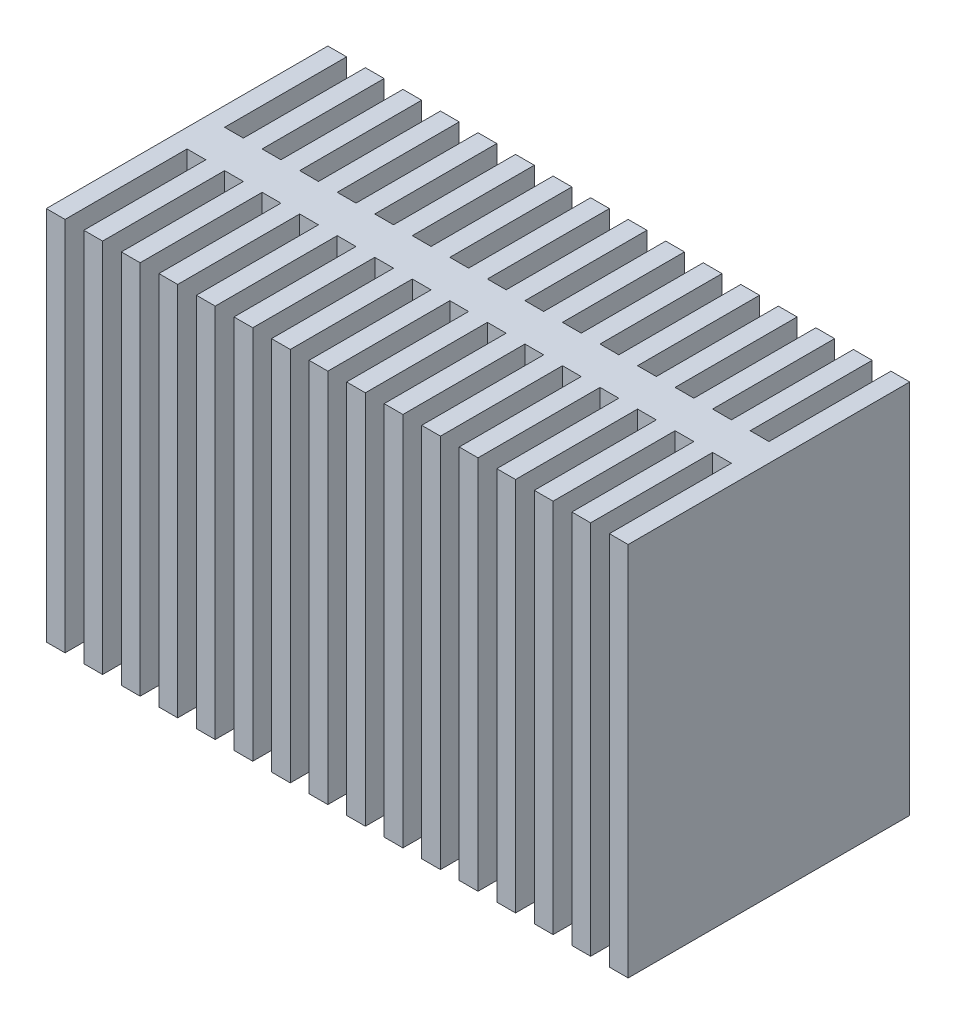
SolidWorks part; units mm, degrees
material "6061 Alloy"
ref_plane "Front Plane" through (0, 0, 0) normal (0, 0, 1) x (1, 0, 0)
ref_plane "Top Plane" through (0, 0, 0) normal (0, 1, 0) x (1, 0, 0)
ref_plane "Right Plane" through (0, 0, 0) normal (1, 0, 0) x (0, 0, -1)
sketch "Sketch2" plane through (0, 0, 0) normal (0, 1, 0) x (1, 0, 0)
  line L0 (0, 0) -> (0, -15)
  line L1 (0, -15) -> (1, -15)
  line L2 (1, -15) -> (1, -8.5)
  line L3 (1, -8.5) -> (2, -8.5)
  line L4 (2, -8.5) -> (2, -6.5)
  line L5 (2, -6.5) -> (1, -6.5)
  line L6 (1, -6.5) -> (1, 0)
  line L7 (1, 0) -> (0, 0)
  line L8 (3, 0) -> (2, 0)
  line L9 (2, 0) -> (2, -15)
  line L10 (2, -15) -> (3, -15)
  line L11 (3, -15) -> (3, -8.5)
  line L12 (3, -8.5) -> (4, -8.5)
  line L13 (4, -8.5) -> (4, -6.5)
  line L14 (4, -6.5) -> (3, -6.5)
  line L15 (3, -6.5) -> (3, 0)
  line L16 (5, 0) -> (4, 0)
  line L17 (4, 0) -> (4, -15)
  line L18 (4, -15) -> (5, -15)
  line L19 (5, -15) -> (5, -8.5)
  line L20 (5, -8.5) -> (6, -8.5)
  line L21 (6, -8.5) -> (6, -6.5)
  line L22 (6, -6.5) -> (5, -6.5)
  line L23 (5, -6.5) -> (5, 0)
  line L24 (7, 0) -> (6, 0)
  line L25 (6, 0) -> (6, -15)
  line L26 (6, -15) -> (7, -15)
  line L27 (7, -15) -> (7, -8.5)
  line L28 (7, -8.5) -> (8, -8.5)
  line L29 (8, -8.5) -> (8, -6.5)
  line L30 (8, -6.5) -> (7, -6.5)
  line L31 (7, -6.5) -> (7, 0)
  line L32 (9, 0) -> (8, 0)
  line L33 (8, 0) -> (8, -15)
  line L34 (8, -15) -> (9, -15)
  line L35 (9, -15) -> (9, -8.5)
  line L36 (9, -8.5) -> (10, -8.5)
  line L37 (10, -8.5) -> (10, -6.5)
  line L38 (10, -6.5) -> (9, -6.5)
  line L39 (9, -6.5) -> (9, 0)
  line L40 (11, 0) -> (10, 0)
  line L41 (10, 0) -> (10, -15)
  line L42 (10, -15) -> (11, -15)
  line L43 (11, -15) -> (11, -8.5)
  line L44 (11, -8.5) -> (12, -8.5)
  line L45 (12, -8.5) -> (12, -6.5)
  line L46 (12, -6.5) -> (11, -6.5)
  line L47 (11, -6.5) -> (11, 0)
  line L48 (12, -15) -> (12, 0)
  line L49 (12, 0) -> (13, 0)
  line L50 (13, 0) -> (13, -15)
  line L51 (13, -15) -> (12, -15)
  line L52 (13, 0) -> (12, 0)
  line L53 (12, 0) -> (12, -15)
  line L54 (12, -15) -> (13, -15)
  line L55 (13, -15) -> (13, -8.5)
  line L56 (13, -8.5) -> (14, -8.5)
  line L57 (14, -8.5) -> (14, -6.5)
  line L58 (14, -6.5) -> (13, -6.5)
  line L59 (13, -6.5) -> (13, 0)
  line L60 (15, 0) -> (14, 0)
  line L61 (14, 0) -> (14, -15)
  line L62 (14, -15) -> (15, -15)
  line L63 (15, -15) -> (15, -8.5)
  line L64 (15, -8.5) -> (16, -8.5)
  line L65 (16, -8.5) -> (16, -6.5)
  line L66 (16, -6.5) -> (15, -6.5)
  line L67 (15, -6.5) -> (15, 0)
  line L68 (17, 0) -> (16, 0)
  line L69 (16, 0) -> (16, -15)
  line L70 (16, -15) -> (17, -15)
  line L71 (17, -15) -> (17, -8.5)
  line L72 (17, -8.5) -> (18, -8.5)
  line L73 (18, -8.5) -> (18, -6.5)
  line L74 (18, -6.5) -> (17, -6.5)
  line L75 (17, -6.5) -> (17, 0)
  line L76 (19, 0) -> (18, 0)
  line L77 (18, 0) -> (18, -15)
  line L78 (18, -15) -> (19, -15)
  line L79 (19, -15) -> (19, -8.5)
  line L80 (19, -8.5) -> (20, -8.5)
  line L81 (20, -8.5) -> (20, -6.5)
  line L82 (20, -6.5) -> (19, -6.5)
  line L83 (19, -6.5) -> (19, 0)
  line L84 (21, 0) -> (20, 0)
  line L85 (20, 0) -> (20, -15)
  line L86 (20, -15) -> (21, -15)
  line L87 (21, -15) -> (21, -8.5)
  line L88 (21, -8.5) -> (22, -8.5)
  line L89 (22, -8.5) -> (22, -6.5)
  line L90 (22, -6.5) -> (21, -6.5)
  line L91 (21, -6.5) -> (21, 0)
  line L92 (23, 0) -> (22, 0)
  line L93 (22, 0) -> (22, -15)
  line L94 (22, -15) -> (23, -15)
  line L95 (23, -15) -> (23, -8.5)
  line L96 (23, -8.5) -> (24, -8.5)
  line L97 (24, -8.5) -> (24, -6.5)
  line L98 (24, -6.5) -> (23, -6.5)
  line L99 (23, -6.5) -> (23, 0)
  line L100 (25, 0) -> (24, 0)
  line L101 (24, 0) -> (24, -15)
  line L102 (24, -15) -> (25, -15)
  line L103 (25, -15) -> (25, -8.5)
  line L104 (25, -8.5) -> (26, -8.5)
  line L105 (26, -8.5) -> (26, -6.5)
  line L106 (26, -6.5) -> (25, -6.5)
  line L107 (25, -6.5) -> (25, 0)
  line L108 (27, 0) -> (26, 0)
  line L109 (26, 0) -> (26, -15)
  line L110 (26, -15) -> (27, -15)
  line L111 (27, -15) -> (27, -8.5)
  line L112 (27, -8.5) -> (28, -8.5)
  line L113 (28, -8.5) -> (28, -6.5)
  line L114 (28, -6.5) -> (27, -6.5)
  line L115 (27, -6.5) -> (27, 0)
  line L116 (29, 0) -> (28, 0)
  line L117 (28, 0) -> (28, -15)
  line L118 (28, -15) -> (29, -15)
  line L119 (29, -15) -> (29, -8.5)
  line L120 (29, -8.5) -> (30, -8.5)
  line L121 (30, -8.5) -> (30, -6.5)
  line L122 (30, -6.5) -> (29, -6.5)
  line L123 (29, -6.5) -> (29, 0)
  line L124 (30, -8.5) -> (30, -15)
  line L125 (30, -15) -> (31, -15)
  line L126 (31, -15) -> (31, 0)
  line L127 (31, 0) -> (30, 0)
  line L128 (30, 0) -> (30, -6.5)
  line L129 (30, -6.5) -> (30, -8.5)
  line L130 (30, 0) -> (30, -15)
  dimension "D1" = 15
  dimension "D2" = 2
  dimension "D3" = 6.5
  dimension "D4" = 1
  dimension "D5" = 1
  dimension "D6" = 2
  dimension "D7" = 15
extrude "Boss-Extrude1" add sketch "Sketch2" along normal blind 20 contours L6 L7 L0 L1 L2 L3 L4 L5 | L14 L15 L8 L9 L4 L10 L11 L12 L13 | L22 L23 L16 L17 L13 L18 L19 L20 L21 | L30 L31 L24 L25 L21 L26 L27 L28 L29 | L38 L39 L32 L33 L29 L34 L35 L36 L37 | L46 L47 L40 L41 L37 L42 L43 L44 L45 | L51 L50 L49 L48 L45 | L127 L128 L121 L124 L125 L126 | L52 L53 L54 L55 L56 L57 L58 L59 | L60 L61 L62 L63 L64 L65 L66 L67 | L68 L69 L70 L71 L72 L73 L74 L75 | L76 L77 L78 L79 L80 L81 L82 L83 | L84 L85 L86 L87 L88 L89 L90 L91 | L92 L93 L94 L95 L96 L97 L98 L99 | L100 L101 L102 L103 L104 L105 L106 L107 | L108 L109 L110 L111 L112 L113 L114 L115
